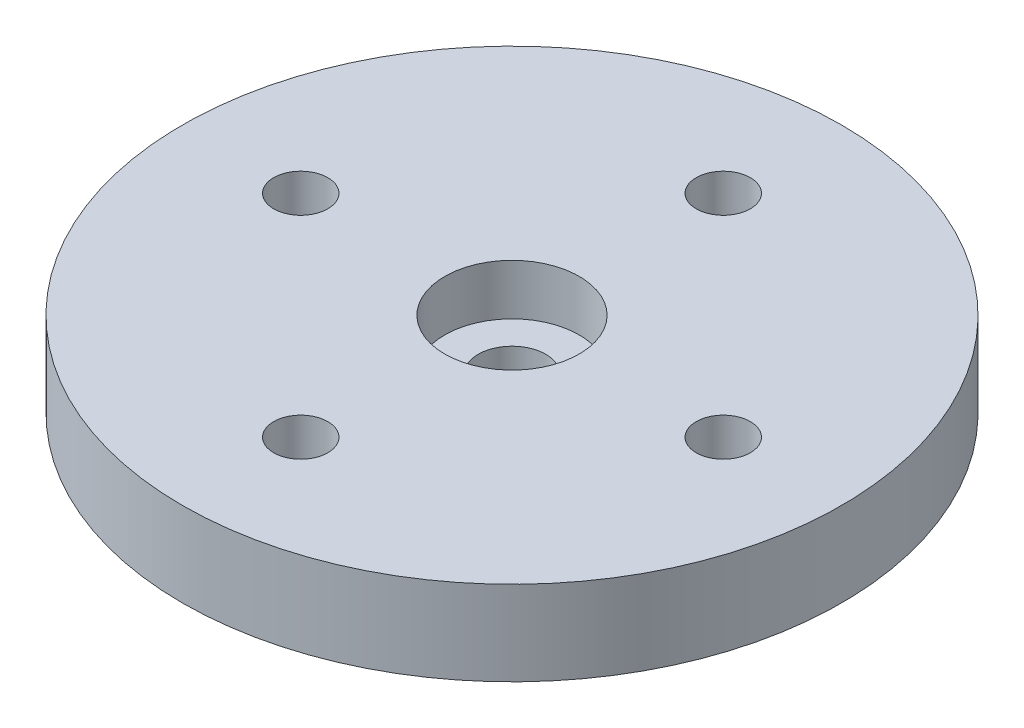
SolidWorks part; units mm, degrees
ref_plane "Front Plane" through (0, 0, 0) normal (0, 0, 1) x (1, 0, 0)
ref_plane "Top Plane" through (0, 0, 0) normal (0, 1, 0) x (1, 0, 0)
ref_plane "Right Plane" through (0, 0, 0) normal (1, 0, 0) x (0, 0, -1)
sketch "Sketch1" plane through (0, 0, 0) normal (0, 1, 0) x (1, 0, 0)
  circle A0 centre (0, 0) radius 19.5
  dimension "D1" = 39
extrude "Boss-Extrude1" add sketch "Sketch1" along normal blind 5
sketch "Sketch2" plane through (0, 5, 0) normal (0, 1, 0) x (1, 0, 0)
  circle A0 centre (0, 0) radius 3.98
  dimension "D1" = 7.96
extrude "Cut-Extrude1" cut sketch "Sketch2" against normal blind 3
sketch "Sketch3" plane through (0, 2, 0) normal (0, 1, 0) x (1, 0, 0)
  circle A0 centre (0, 0) radius 2
  dimension "D1" = 4
extrude "Cut-Extrude2" cut sketch "Sketch3" against normal blind 3
sketch "Sketch4" plane through (0, 5, 0) normal (0, 1, 0) x (1, 0, 0)
  circle A0 centre (0, 0) radius 12.5 construction
  circle A1 centre (0, 12.5) radius 1.6
  dimension "D1" = 25
  dimension "D2" = 3.2
extrude "Cut-Extrude3" cut sketch "Sketch4" against normal through all
pattern_circular "CirPattern1" count 4 over 360 about axis through (0, 0, 0) along (0, 1, 0) of "Cut-Extrude3"
